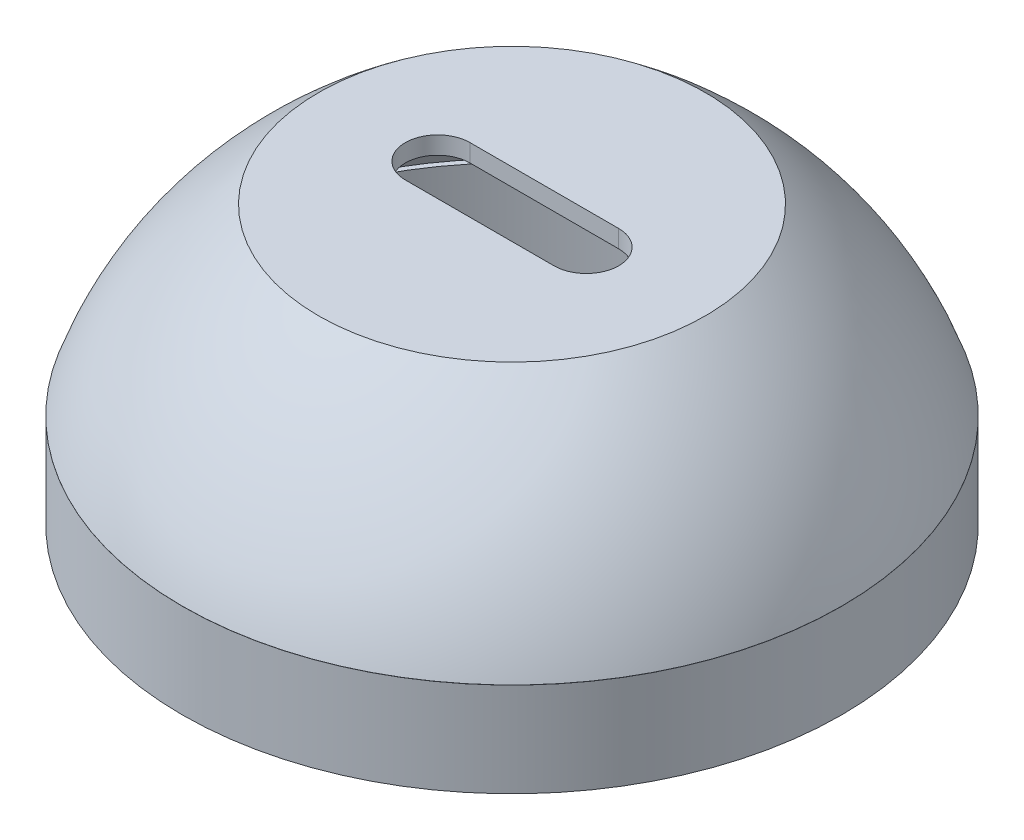
SolidWorks part; units mm, degrees
ref_plane "Front Plane" through (0, 0, 0) normal (0, 0, 1) x (1, 0, 0)
ref_plane "Top Plane" through (0, 0, 0) normal (0, 1, 0) x (1, 0, 0)
ref_plane "Right Plane" through (0, 0, 0) normal (1, 0, 0) x (0, 0, -1)
sketch "Sketch2" plane through (0, 0, 0) normal (0, 0, 1) x (1, 0, 0)
  line L0 (0, 0) -> (29, 0)
  line L2 (0, 0) -> (0, -2.6435)
  line L3 (0, -2.6435) -> (27.5909, -2.6435)
  line L4 (0, 39.6926) -> (0, -78.1016) construction
  line L5 (47.2249, -27.474) -> (49.4329, -27.474)
  spline S0 degree 2 poles (29, 0) (43.9739, -11.4036) (49.4329, -27.474) knots 0 0 0 0.848255 0.848255 0.848255
  spline S1 degree 2 poles (47.2249, -27.474) (40.2352, -12.0813) (27.5909, -2.6435) knots 0 0 0 0.915288 0.915288 0.915288
  dimension "D2" = 29
revolve "Revolve1" add sketch "Sketch2" angle 360 about L4
sketch "Sketch3" plane through (0, 0, 0) normal (0, 0, 1) x (1, 0, 0)
  line L0 (46.468, -27.4917) -> (49.4329, -27.4917)
  line L1 (49.4329, -27.4917) -> (49.4329, -41.6007)
  line L2 (49.4329, -41.6007) -> (46.468, -41.6007)
  line L3 (46.468, -41.6007) -> (46.468, -27.4917)
  line L4 (0, 0) -> (0, -64.3629) construction
revolve "Revolve2" add sketch "Sketch3" angle 360 about L4
sketch "Sketch6" plane through (0, 0, 0) normal (0, 1, 0) x (1, 0, 0)
  line L0 (-11.15, 0) -> (11.15, 0) construction
  line L1 (-22.8804, 0) -> (22.8804, 0) construction
  line L2 (-11.15, 4.85) -> (11.15, 4.85)
  line L3 (-11.15, -4.85) -> (11.15, -4.85)
  arc A0 (-11.15, 4.85) -> (-11.15, -4.85) centre (-11.15, 0) ccw
  arc A1 (11.15, -4.85) -> (11.15, 4.85) centre (11.15, 0) ccw
  point P5 (0, 0)
  point P10 (0, 0)
  dimension "D1" = 4.85
  dimension "D2" = 22.3
extrude "Cut-Extrude3" cut sketch "Sketch6" against normal blind 10
